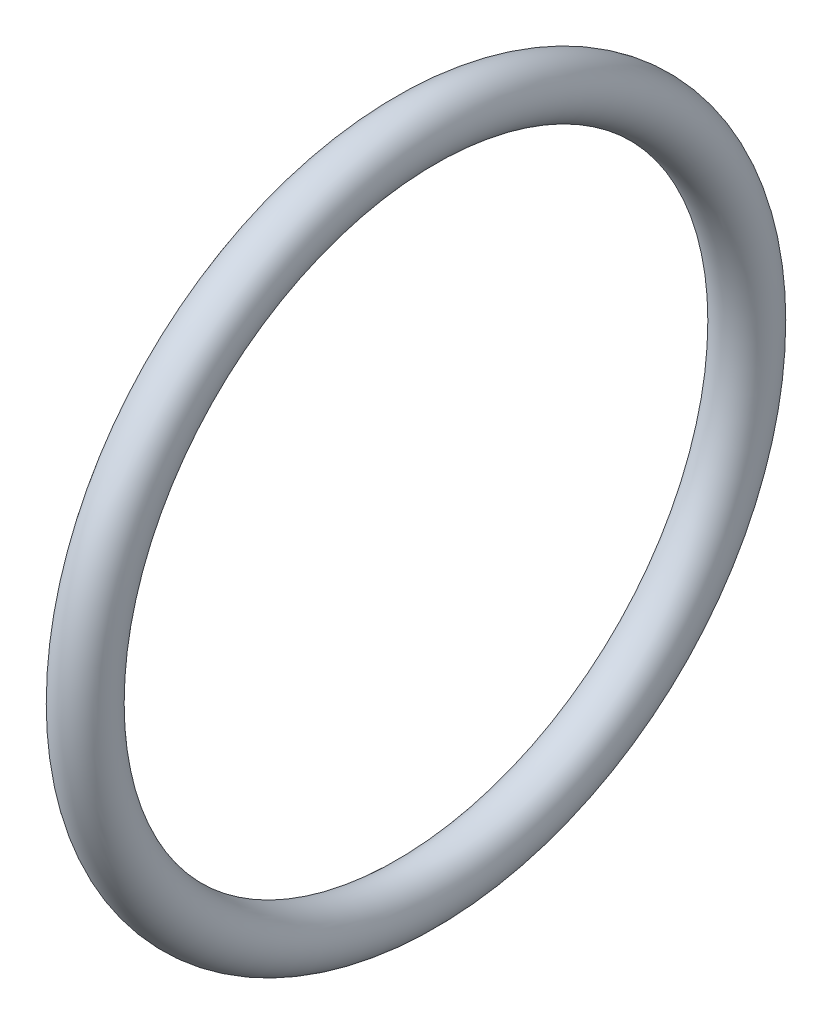
SolidWorks part; units mm, degrees
ref_plane "Front Plane" through (0, 0, 0) normal (0, 0, 1) x (1, 0, 0)
ref_plane "Top Plane" through (0, 0, 0) normal (0, 1, 0) x (1, 0, 0)
ref_plane "Right Plane" through (0, 0, 0) normal (1, 0, 0) x (0, 0, -1)
sketch "Sketch1" plane through (0, 0, 0) normal (0, 0, 1) x (1, 0, 0)
  line L0 (-22.6286, 0) -> (36.4571, 0) construction
  line L1 (0, 0) -> (0, 12) construction
  circle A0 centre (0, 12) radius 1
  dimension "D2" = 2
  dimension "D1" = 12
revolve "Revolve1" add sketch "Sketch1" angle 360 about L0
